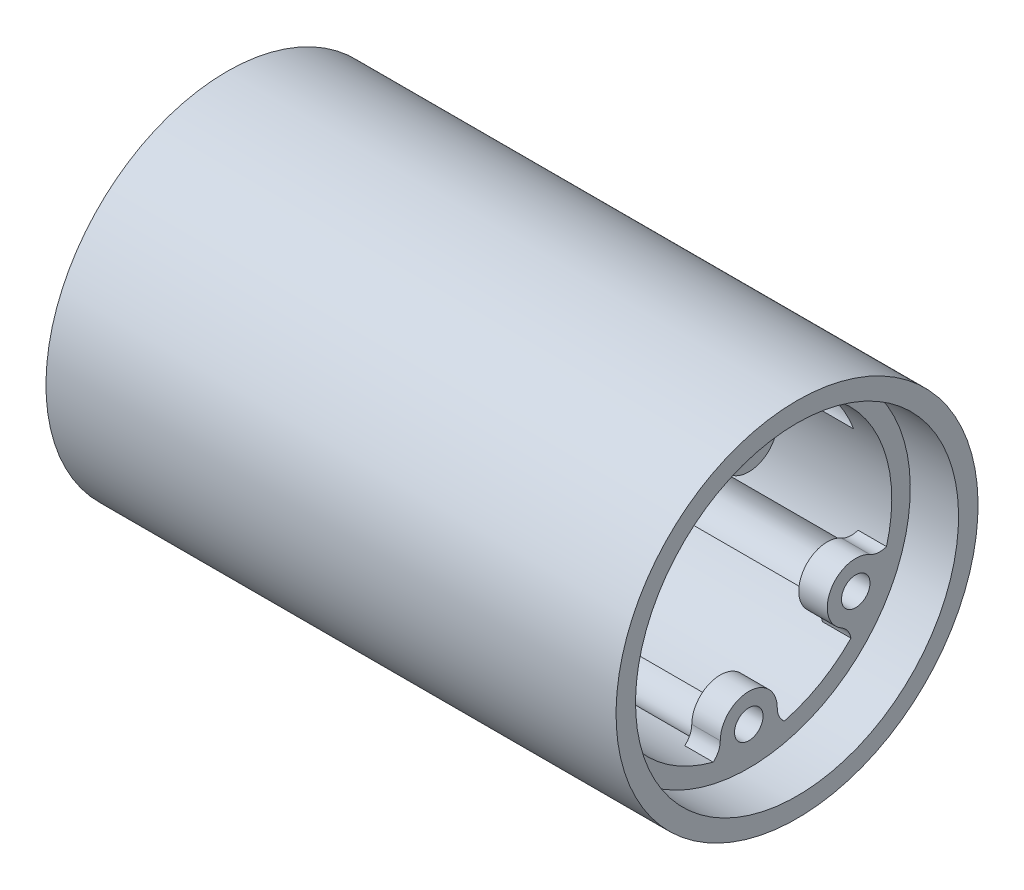
SolidWorks part; units mm, degrees
material "6061-T6 (SS)"
ref_plane "Front Plane" through (0, 0, 0) normal (0, 0, 1) x (1, 0, 0)
ref_plane "Top Plane" through (0, 0, 0) normal (0, 1, 0) x (1, 0, 0)
ref_plane "Right Plane" through (0, 0, 0) normal (1, 0, 0) x (0, 0, -1)
sketch "Sketch1" plane through (0, 0, 0) normal (0, 0, 1) x (1, 0, 0)
  line L0 (0, 0) -> (-40.7053, 0) construction
  line L1 (30, 19.05) -> (-30, 19.05)
  line L2 (30, 19.05) -> (30, 17)
  line L3 (30, 17) -> (-30, 17)
  line L4 (-30, 19.05) -> (-30, 17)
  line L5 (23.65, 17) -> (-23.65, 17)
  line L6 (23.65, 17) -> (23.65, 15.05)
  line L7 (23.65, 15.05) -> (-23.65, 15.05)
  line L8 (-23.65, 17) -> (-23.65, 15.05)
  line L11 (-23.65, 15.05) -> (-23.65, 17)
  line L12 (-23.65, 17) -> (-30, 17)
  line L13 (-30, 15.05) -> (-30, 17)
  line L18 (23.65, 15.05) -> (24.92, 15.05)
  line L19 (23.65, 15.05) -> (23.65, 17)
  line L20 (23.65, 17) -> (24.92, 17)
  line L21 (24.92, 15.05) -> (24.92, 17)
  line L22 (-30, 17) -> (-23.65, 17)
  line L23 (-30, 17) -> (-30, 15.05)
  line L24 (-30, 15.05) -> (-23.65, 15.05)
  line L25 (-23.65, 17) -> (-23.65, 15.05)
  point P8 (0, 15.05)
  point P10 (0, 17)
  dimension "D1" = 19.05
  dimension "D2" = 17
  dimension "D3" = 6.35
  dimension "D4" = 60
  dimension "D5" = 4
  dimension "D6" = 5.08
revolve "Revolve1" add sketch "Sketch1" angle 360 about L0
sketch "Sketch2" plane through (24.92, 0, 0) normal (1, 0, 0) x (0, 0, -1)
  line L0 (-3, 13) -> (-3, 7.4251) construction
  arc A0 (-3, 13) -> (3, 13) centre (0, 13) ccw
  circle A1 centre (0, 0) radius 16 construction
  circle A2 centre (0, 13) radius 1.5
  arc A3 (-3, 13) -> (-5.7962, 14.9132) centre (-5.0526, 13) ccw
  arc A4 (3, 13) -> (5.7962, 14.9132) centre (5.0526, 13) cw
  arc A5 (9.7583, 9.0981) -> (10.0171, 12.4763) centre (8.732, 10.8757) ccw
  arc A6 (9.7583, 9.0981) -> (12.7583, 3.9019) centre (11.2583, 6.5) ccw
  arc A7 (12.7583, 3.9019) -> (15.8133, 2.4369) centre (13.7846, 2.1243) cw
  circle A8 centre (11.2583, 6.5) radius 1.5
  arc A9 (12.7583, -3.9019) -> (15.8133, -2.4369) centre (13.7846, -2.1243) ccw
  arc A10 (12.7583, -3.9019) -> (9.7583, -9.0981) centre (11.2583, -6.5) ccw
  arc A11 (9.7583, -9.0981) -> (10.0171, -12.4763) centre (8.732, -10.8757) cw
  circle A12 centre (11.2583, -6.5) radius 1.5
  arc A13 (3, -13) -> (5.7962, -14.9132) centre (5.0526, -13) ccw
  arc A14 (3, -13) -> (-3, -13) centre (0, -13) ccw
  arc A15 (-3, -13) -> (-5.7962, -14.9132) centre (-5.0526, -13) cw
  circle A16 centre (0, -13) radius 1.5
  arc A17 (-9.7583, -9.0981) -> (-10.0171, -12.4763) centre (-8.732, -10.8757) ccw
  arc A18 (-9.7583, -9.0981) -> (-12.7583, -3.9019) centre (-11.2583, -6.5) ccw
  arc A19 (-12.7583, -3.9019) -> (-15.8133, -2.4369) centre (-13.7846, -2.1243) cw
  circle A20 centre (-11.2583, -6.5) radius 1.5
  arc A21 (-12.7583, 3.9019) -> (-15.8133, 2.4369) centre (-13.7846, 2.1243) ccw
  arc A22 (-12.7583, 3.9019) -> (-9.7583, 9.0981) centre (-11.2583, 6.5) ccw
  arc A23 (-9.7583, 9.0981) -> (-10.0171, 12.4763) centre (-8.732, 10.8757) cw
  circle A24 centre (-11.2583, 6.5) radius 1.5
  dimension "D1" = 6
  dimension "D2" = 3
  dimension "D3" = 6
extrude "Boss-Extrude1" add sketch "Sketch2" against normal blind 3 contours A1 L0 A0 A4 A2 | L0 A1 A3 | A10 A11 A1 A9 A12 | A14 L0 A1 A13 A16 | L0 A15 A1 | A22 A23 A1 A21 A24
sketch "Sketch5" plane through (-30, 0, 0) normal (-1, 0, 0) x (0, 0, 1)
  line L0 (7.4838, 12.9623) -> (4.0096, 6.9449) construction
  line L1 (0, 10) -> (0, 19.05)
  line L2 (8.6603, 5) -> (16.4978, 9.525)
  line L3 (9.525, 16.4978) -> (7.525, 13.0337)
  circle A0 centre (-17.05, 0) radius 1.5
  circle A1 centre (0, 0) radius 19.05 construction
  arc A2 (-3, 13) -> (3, 13) centre (0, 13) ccw construction
  circle A3 centre (0, 0) radius 17.05 construction
  circle A4 centre (-8.525, 14.7657) radius 1.5
  circle A5 centre (8.525, 14.7657) radius 1.5
  circle A6 centre (17.05, 0) radius 1.5
  circle A7 centre (8.525, -14.7657) radius 1.5
  circle A8 centre (-8.525, -14.7657) radius 1.5
  circle A9 centre (0, 0) radius 15.05 construction
  arc A11 (9.7583, 9.0981) -> (12.7583, 3.9019) centre (11.2583, 6.5) ccw construction
  point P34 (0, 0)
  point P35 (8.525, 14.7657)
  dimension "D1" = 3
  dimension "D3" = 300
  dimension "D4" = 30
  dimension "D2" = 6
extrude "Cut-Extrude1" cut sketch "Sketch5" against normal blind 10 contours A8 | A7 | A6 | A0 | A5 | A4
sketch "Sketch6" plane through (-30, 0, 0) normal (-1, 0, 0) x (0, 0, 1)
  circle A0 centre (0, 13) radius 3
  circle A1 centre (11.2583, 6.5) radius 3
  circle A2 centre (0, -13) radius 3
  circle A3 centre (-11.2583, -6.5) radius 3
  circle A6 centre (-11.2583, 6.5) radius 3
  circle A7 centre (0, 13) radius 3
  circle A8 centre (11.2583, 6.5) radius 3
  circle A9 centre (11.2583, -6.5) radius 3
  circle A10 centre (0, -13) radius 3
  circle M9 centre (0, 0) radius 15.05
  dimension "D1" = 6
  dimension "D2" = 6
  dimension "D3" = 6
  dimension "D4" = 6
  dimension "D5" = 6
extrude "Cut-Extrude2" cut sketch "Sketch6" against normal up to surface (51.92 mm away) contours A6 M9 | A6 M9 | A0 M9 | A1 M9 | A1 M9 | A9 M9 | A9 M9 | A2 M9 | A2 M9 | A3 M9 | A3 M9 up to face at (21.92, 14.5, 0)
